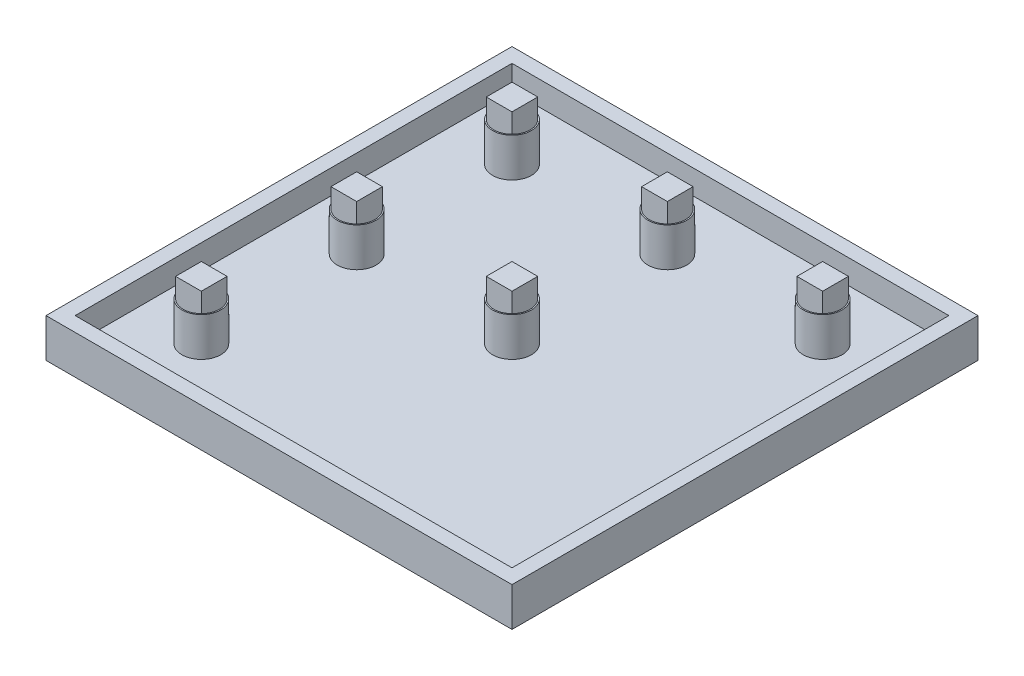
SolidWorks part; units mm, degrees
ref_plane "Front Plane" through (0, 0, 0) normal (0, 0, 1) x (1, 0, 0)
ref_plane "Top Plane" through (0, 0, 0) normal (0, 1, 0) x (1, 0, 0)
ref_plane "Right Plane" through (0, 0, 0) normal (1, 0, 0) x (0, 0, -1)
sketch "Sketch1" plane through (0, 0, 0) normal (0, 1, 0) x (1, 0, 0)
  line L1 (0, 0) -> (1219.2, 0)
  line L2 (0, 0) -> (0, 1219.2)
  line L3 (0, 1219.2) -> (1219.2, 1219.2)
  line L4 (1219.2, 0) -> (1219.2, 1219.2)
  dimension "D1" = 1219.2
  dimension "D2" = 1219.2
extrude "Boss-Extrude1" add sketch "Sketch1" along normal blind 101.6
shell "Shell2" thickness 38.1
sketch "Sketch3" plane through (0, 38.1, 0) normal (0, 1, 0) x (1, 0, 0)
  line L0 (0, 0) -> (1219.2, 0) construction
  line L1 (1219.2, 1219.2) -> (0, 1219.2) construction
  line L2 (0, 1219.2) -> (0, 0) construction
  circle A0 centre (203.2, 1016) radius 50.8
  circle A1 centre (609.6, 1016) radius 50.8
  circle A2 centre (1016, 1016) radius 50.8
  circle A3 centre (203.2, 609.6) radius 50.8
  circle A4 centre (609.6, 609.6) radius 50.8
  circle A5 centre (203.2, 203.2) radius 50.8
  dimension "D1" = 101.6
  dimension "D2" = 101.6
  dimension "D3" = 101.6
  dimension "D4" = 101.6
  dimension "D5" = 101.6
  dimension "D6" = 101.6
  dimension "D7" = 406.4
  dimension "D8" = 406.4
  dimension "D9" = 203.2
  dimension "D10" = 203.2
  dimension "D11" = 406.4
  dimension "D12" = 406.4
  dimension "D13" = 406.4
  dimension "D14" = 406.4
  dimension "D15" = 203.2
  dimension "D16" = 203.2
  dimension "D17" = 203.2
  dimension "D18" = 203.2
extrude "Boss-Extrude5" add sketch "Sketch3" along normal blind 101.6
shell "Shell3" thickness 3.175
sketch "Sketch4" plane through (0, 139.7, 0) normal (0, 1, 0) x (1, 0, 0)
  line L1 (236.8969, 643.255) -> (169.5031, 643.255)
  line L2 (236.8969, 643.255) -> (236.8969, 575.945)
  line L3 (236.8969, 575.945) -> (169.5031, 575.945)
  line L4 (169.5031, 643.255) -> (169.5031, 575.945)
  line L5 (236.8969, 643.255) -> (169.5031, 575.945) construction
  line L6 (236.8969, 575.945) -> (169.5031, 643.255) construction
  circle A0 centre (203.2, 609.6) radius 47.625 construction
  point P0 (203.2, 609.6)
  dimension "D1" = 67.31
extrude "Boss-Extrude7" add sketch "Sketch4" along normal mid plane 101.6 separate body
sketch "Sketch5" plane through (0, 139.7, 0) normal (0, 1, 0) x (1, 0, 0)
  line L1 (169.5432, 236.8951) -> (236.8568, 236.8951)
  line L2 (169.5432, 236.8951) -> (169.5432, 169.5049)
  line L3 (169.5432, 169.5049) -> (236.8568, 169.5049)
  line L4 (236.8568, 236.8951) -> (236.8568, 169.5049)
  line L5 (169.5432, 236.8951) -> (236.8568, 169.5049) construction
  line L6 (169.5432, 169.5049) -> (236.8568, 236.8951) construction
  circle A0 centre (203.2, 203.2) radius 47.625 construction
  point P0 (203.2, 203.2)
extrude "Boss-Extrude8" add sketch "Sketch5" along normal mid plane 101.6 separate body
sketch "Sketch6" plane through (0, 139.7, 0) normal (0, 1, 0) x (1, 0, 0)
  line L1 (169.545, 1049.6969) -> (236.855, 1049.6969)
  line L2 (169.545, 1049.6969) -> (169.545, 982.3031)
  line L3 (169.545, 982.3031) -> (236.855, 982.3031)
  line L4 (236.855, 1049.6969) -> (236.855, 982.3031)
  line L5 (169.545, 1049.6969) -> (236.855, 982.3031) construction
  line L6 (169.545, 982.3031) -> (236.855, 1049.6969) construction
  circle A0 centre (203.2, 1016) radius 47.625 construction
  point P2 (203.2, 1016)
  dimension "D1" = 67.31
extrude "Boss-Extrude9" add sketch "Sketch6" along normal mid plane 101.6 separate body
sketch "Sketch8" plane through (0, 139.7, 0) normal (0, 1, 0) x (1, 0, 0)
  line L1 (575.9212, 1049.6731) -> (643.2788, 1049.6731)
  line L2 (575.9212, 1049.6731) -> (575.9212, 982.3269)
  line L3 (575.9212, 982.3269) -> (643.2788, 982.3269)
  line L4 (643.2788, 1049.6731) -> (643.2788, 982.3269)
  line L5 (575.9212, 1049.6731) -> (643.2788, 982.3269) construction
  line L6 (575.9212, 982.3269) -> (643.2788, 1049.6731) construction
  circle A0 centre (609.6, 1016) radius 47.625 construction
  point P0 (609.6, 1016)
extrude "Boss-Extrude10" add sketch "Sketch8" along normal mid plane 101.6 separate body
sketch "Sketch9" plane through (0, 139.7, 0) normal (0, 1, 0) x (1, 0, 0)
  line L1 (575.8901, 643.242) -> (643.3099, 643.242)
  line L2 (575.8901, 643.242) -> (575.8901, 575.958)
  line L3 (575.8901, 575.958) -> (643.3099, 575.958)
  line L4 (643.3099, 643.242) -> (643.3099, 575.958)
  line L5 (575.8901, 643.242) -> (643.3099, 575.958) construction
  line L6 (575.8901, 575.958) -> (643.3099, 643.242) construction
  circle A0 centre (609.6, 609.6) radius 47.625 construction
  point P0 (609.6, 609.6)
extrude "Boss-Extrude11" add sketch "Sketch9" along normal mid plane 101.6 separate body
sketch "Sketch10" plane through (0, 139.7, 0) normal (0, 1, 0) x (1, 0, 0)
  line L1 (982.3374, 1049.6893) -> (1049.6626, 1049.6893)
  line L2 (982.3374, 1049.6893) -> (982.3374, 982.3107)
  line L3 (982.3374, 982.3107) -> (1049.6626, 982.3107)
  line L4 (1049.6626, 1049.6893) -> (1049.6626, 982.3107)
  line L5 (982.3374, 1049.6893) -> (1049.6626, 982.3107) construction
  line L6 (982.3374, 982.3107) -> (1049.6626, 1049.6893) construction
  circle A0 centre (1016, 1016) radius 47.625 construction
  point P0 (1016, 1016)
extrude "Boss-Extrude12" add sketch "Sketch10" along normal mid plane 101.6 separate body
